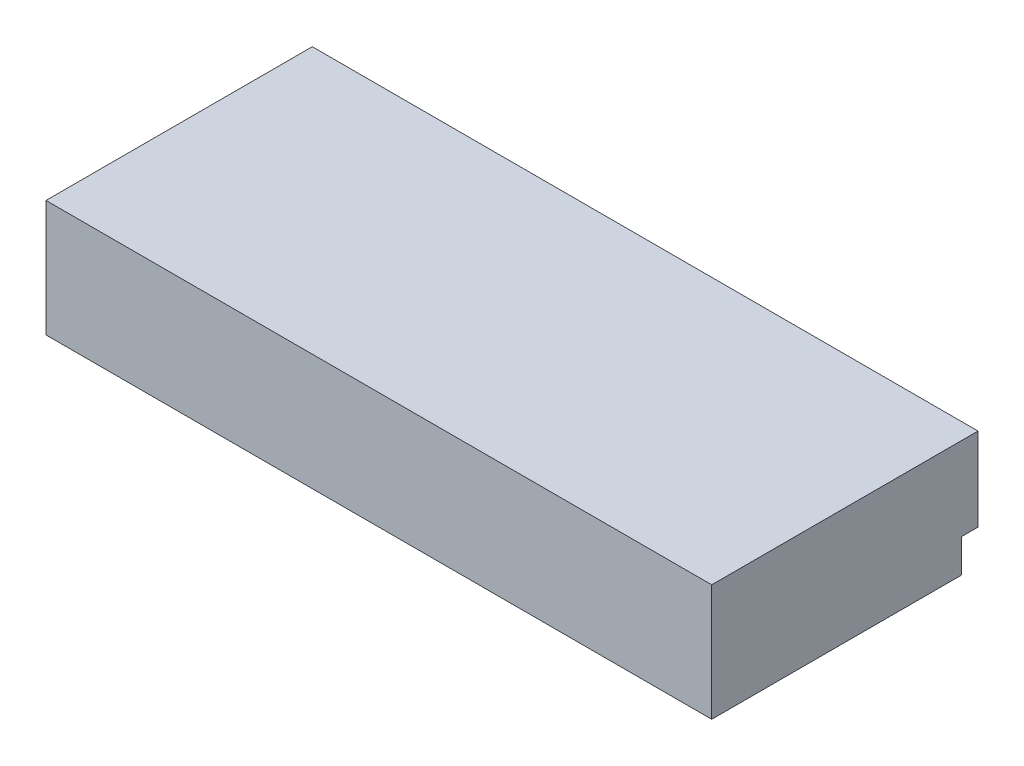
SolidWorks part; units mm, degrees
material "Plain Carbon Steel"
ref_plane "Front Plane" through (0, 0, 0) normal (0, 0, 1) x (1, 0, 0)
ref_plane "Top Plane" through (0, 0, 0) normal (0, 1, 0) x (1, 0, 0)
ref_plane "Right Plane" through (0, 0, 0) normal (1, 0, 0) x (0, 0, -1)
sketch "Sketch1" plane through (0, 0, 0) normal (0, 1, 0) x (1, 0, 0)
  line L1 (-100, -40) -> (100, -40)
  line L2 (-100, -40) -> (-100, 40)
  line L3 (-100, 40) -> (100, 40)
  line L4 (100, -40) -> (100, 40)
  line L5 (-100, -40) -> (100, 40) construction
  line L6 (-100, 40) -> (100, -40) construction
  point P0 (0, 0)
  dimension "D1" = 200
  dimension "D2" = 80
extrude "Boss-Extrude1" add sketch "Sketch1" along normal blind 35
sketch "Sketch2" plane through (100, 0, 0) normal (1, 0, 0) x (0, 0, -1)
  line L1 (40, 0) -> (35, 0)
  line L2 (40, 0) -> (40, 10)
  line L3 (40, 10) -> (35, 10)
  line L4 (35, 0) -> (35, 10)
  dimension "D1" = 10
  dimension "D2" = 5
extrude "Cut-Extrude1" cut sketch "Sketch2" against normal through all
sketch "Sketch3" [suppressed] plane through (0, 35, 0) normal (0, 1, 0) x (1, 0, 0)
  circle A0 centre (-62, -40) radius 31
  circle A1 centre (38, -40) radius 55
extrude "Cut-Extrude2" [suppressed] cut sketch "Sketch3" against normal through all
sketch "Sketch4" [suppressed] plane through (0, 35, 0) normal (0, 1, 0) x (1, 0, 0)
  circle A0 centre (-38, -40) radius 55
  circle A1 centre (62, -40) radius 31
extrude "Cut-Extrude3" [suppressed] cut sketch "Sketch4" against normal through all
sketch "Sketch5" [suppressed] plane through (0, 35, 0) normal (0, 1, 0) x (1, 0, 0)
  point P0 (-87, 22)
  point P1 (0, 22)
  point P3 (87, 22)
  point P5 (67, 22)
hole_wizard "Ø12.0mm Dowel Hole2" [suppressed] positions "Sketch6" profile "Sketch7" hole size "Ø12.0" standard "ISO"
sketch "Sketch6" plane through (0, 35, 0) normal (0, 1, 0) x (1, 0, 0)
  point P0 (-87, 22)
  point P3 (0, 22)
  point P6 (87, 22)
sketch "Sketch7" plane through (-87, 35, -22) normal (1, 0, 0) x (0, 0, 1)
  line L0 (0, 0) -> (0, 28.0644)
  line L1 (0, 28.0644) -> (5.1, 25)
  line L2 (5.1, 25) -> (5.1, 0)
  line L5 (5.1, 0) -> (0, 0)
  line L10 (0, 28.0644) -> (-5.1, 25) construction
  line L11 (0, -6.35) -> (0, 107.95) construction
  dimension "Hole Dia." = 10.2
  dimension "Hole Depth" = 25
  dimension "Drill Angle" = 118
hole_wizard "Ø6.0mm Dowel Hole1" [suppressed] positions "Sketch8" profile "Sketch9" hole size "Ø6.0" standard "ISO"
sketch "Sketch8" plane through (0, 35, 0) normal (0, 1, 0) x (1, 0, 0)
  point P0 (67, 22)
sketch "Sketch9" plane through (67, 35, -22) normal (1, 0, 0) x (0, 0, 1)
  line L0 (0, 0) -> (0, 11.8026)
  line L1 (0, 11.8026) -> (3, 10)
  line L2 (3, 10) -> (3, 0)
  line L5 (3, 0) -> (0, 0)
  line L10 (0, 11.8026) -> (-3, 10) construction
  line L11 (0, -6.35) -> (0, 107.95) construction
  dimension "Hole Dia." = 6
  dimension "Hole Depth" = 10
  dimension "Drill Angle" = 118
sketch "Sketch10" [suppressed] plane through (0, 35, 0) normal (0, 1, 0) x (1, 0, 0)
  point P0 (-87, 22)
  point P1 (-67, 22)
  point P3 (0, 22)
  point P5 (87, 22)
hole_wizard "Ø6.0mm Dowel Hole2" [suppressed] positions "Sketch11" profile "Sketch12" hole size "Ø6.0" standard "ISO"
sketch "Sketch11" plane through (0, 35, 0) normal (0, 1, 0) x (1, 0, 0)
  point P0 (-67, 22)
sketch "Sketch12" plane through (-67, 35, -22) normal (1, 0, 0) x (0, 0, 1)
  line L0 (0, 0) -> (0, 11.8026)
  line L1 (0, 11.8026) -> (3, 10)
  line L2 (3, 10) -> (3, 0)
  line L5 (3, 0) -> (0, 0)
  line L10 (0, 11.8026) -> (-3, 10) construction
  line L11 (0, -6.35) -> (0, 107.95) construction
  dimension "Hole Dia." = 6
  dimension "Hole Depth" = 10
  dimension "Drill Angle" = 118
hole_wizard "Ø12.0mm Dowel Hole3" [suppressed] positions "Sketch13" profile "Sketch14" hole size "Ø12.0" standard "ISO"
sketch "Sketch13" plane through (0, 35, 0) normal (0, 1, 0) x (1, 0, 0)
  point P0 (-87, 22)
  point P3 (0, 22)
  point P6 (87, 22)
sketch "Sketch14" plane through (-87, 35, -22) normal (1, 0, 0) x (0, 0, 1)
  line L0 (0, 0) -> (0, 28.0644)
  line L1 (0, 28.0644) -> (5.1, 25)
  line L2 (5.1, 25) -> (5.1, 0)
  line L5 (5.1, 0) -> (0, 0)
  line L10 (0, 28.0644) -> (-5.1, 25) construction
  line L11 (0, -6.35) -> (0, 107.95) construction
  dimension "Hole Dia." = 10.2
  dimension "Hole Depth" = 25
  dimension "Drill Angle" = 118
chamfer "Chamfer1" [suppressed] distance 3.5 angle 45
chamfer "Chamfer2" [suppressed] distance 3.5 angle 45
